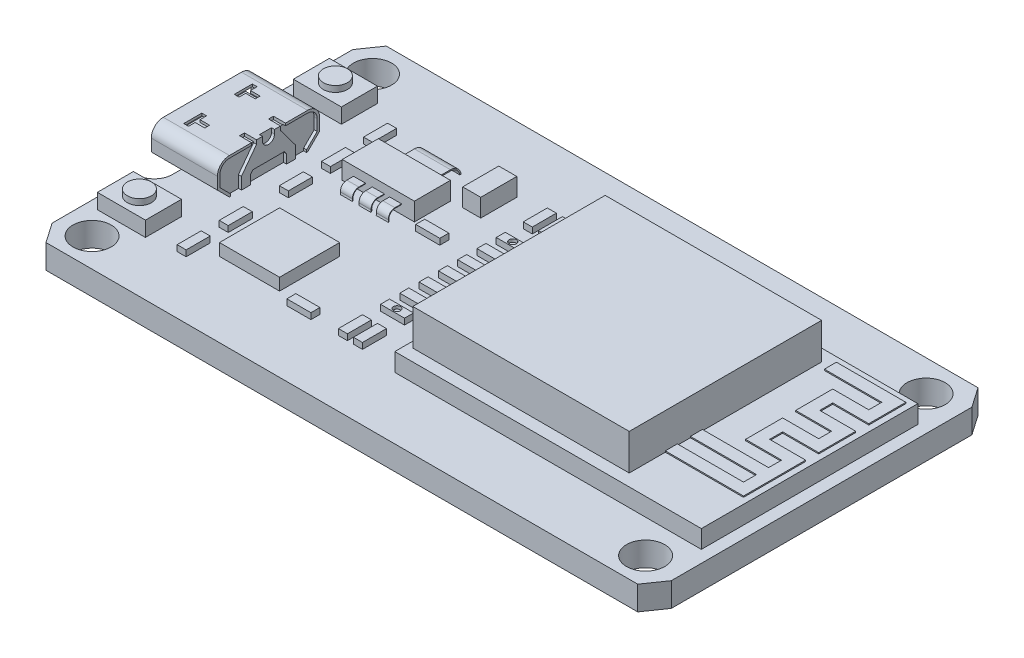
SolidWorks part; units mm, degrees
ref_plane "Alzado" through (0, 0, 0) normal (0, 0, 1) x (1, 0, 0)
ref_plane "Planta" through (0, 0, 0) normal (0, 1, 0) x (1, 0, 0)
ref_plane "Vista lateral" through (0, 0, 0) normal (1, 0, 0) x (0, 0, -1)
sketch "Croquis1" plane through (0, 0, 0) normal (0, 1, 0) x (1, 0, 0)
  line L1 (25.75, 14.15) -> (-25.75, 14.15)
  line L2 (25.75, 14.15) -> (25.75, -14.15)
  line L3 (25.75, -14.15) -> (-25.75, -14.15)
  line L4 (-25.75, 14.15) -> (-25.75, -14.15)
  line L5 (25.75, 14.15) -> (-25.75, -14.15) construction
  line L6 (25.75, -14.15) -> (-25.75, 14.15) construction
  point P0 (0, 0)
  dimension "D1" = 28.3
  dimension "D2" = 51.5
extrude "Saliente-Extruir1" add sketch "Croquis1" along normal blind 2
sketch "Croquis2" plane through (0, 2, 0) normal (0, 1, 0) x (1, 0, 0)
  line L0 (-23.1625, 11.5625) -> (22.875, 11.5625) construction
  line L1 (-23.1625, 11.5625) -> (-25.75, 11.5625) construction
  line L2 (-25.75, 14.15) -> (-25.75, -14.15) construction
  line L3 (-25.75, 11.5625) -> (-24.75, 11.5625) construction
  line L4 (24.4625, 11.5625) -> (25.75, 11.5625) construction
  line L5 (25.75, -14.15) -> (25.75, 14.15) construction
  line L6 (-23.1625, 13.15) -> (-23.1625, 14.15) construction
  line L8 (-23.1625, 11.5625) -> (-23.1625, -11.7625) construction
  line L9 (-23.1625, -11.7625) -> (22.875, -11.7625) construction
  line L10 (25.75, 14.15) -> (-25.75, 14.15) construction
  circle A0 centre (-23.1625, 11.5625) radius 1.5875
  circle A1 centre (22.875, 11.5625) radius 1.5875
  circle A2 centre (-23.1625, -11.7625) radius 1.5875
  circle A3 centre (22.875, -11.7625) radius 1.5875
  point P6 (-0.1437, 11.5625)
  dimension "D1" = 3.175
  dimension "D3" = 1
  dimension "D2" = 46.0375
  dimension "D4" = 1.2875
  dimension "D5" = 23.325
  dimension "D6" = 1
extrude "Cortar-Extruir1" cut sketch "Croquis2" against normal blind 2
sketch "Croquis13" plane through (0, 2, 0) normal (0, 1, 0) x (1, 0, 0)
  line L0 (25.75, 12.5) -> (25.75, -12.5)
  line L1 (25.75, -14.15) -> (25.75, 14.15) construction
  line L2 (-24.6062, -14.15) -> (24.6062, -14.15)
  line L3 (-25.75, -14.15) -> (25.75, -14.15) construction
  line L4 (-24.6062, 14.15) -> (24.6062, 14.15)
  line L5 (25.75, 14.15) -> (-25.75, 14.15) construction
  line L6 (24.6062, 14.15) -> (25.75, 12.5)
  line L7 (25.75, -12.5) -> (24.6062, -14.15)
  line L8 (-25.75, 12.5) -> (-25.75, 5.5)
  line L10 (-25.75, 14.15) -> (-25.75, -14.15) construction
  line L11 (-24.6062, 14.15) -> (-25.75, 12.5)
  line L12 (-25.75, -12.5) -> (-24.6062, -14.15)
  line L13 (-24.25, 4) -> (-24.25, -4)
  line L14 (-25.75, -5.5) -> (-25.75, -12.5)
  arc A0 (-24.25, 4) -> (-25.75, 5.5) centre (-25.75, 4) ccw
  arc A1 (-25.75, -5.5) -> (-24.25, -4) centre (-25.75, -4) ccw
  point P5 (25.75, 0)
  point P11 (0, -14.15)
  point P16 (0, 14.15)
  point P19 (-25.75, 0)
  point P24 (-24.25, 0)
  dimension "D1" = 25
  dimension "D2" = 49.2125
  dimension "D3" = 25
  dimension "D4" = 8
  dimension "D5" = 1.5
extrude "Cortar-Extruir2" cut sketch "Croquis13" against normal blind 3 flip side to cut
sketch "Croquis3" plane through (0, 2, 0) normal (0, 1, 0) x (1, 0, 0)
  line L0 (25.75, -12.5) -> (25.75, 12.5) construction
  line L1 (-0.75, -9) -> (24.75, -9)
  line L2 (-0.75, -9) -> (-0.75, 9)
  line L3 (-0.75, 9) -> (24.75, 9)
  line L4 (24.75, -9) -> (24.75, 9)
  line L5 (-0.75, -9) -> (24.75, 9) construction
  line L6 (-0.75, 9) -> (24.75, -9) construction
  point P0 (12, 0)
  dimension "D1" = 18
  dimension "D2" = 25.5
  dimension "D3" = 1
extrude "Saliente-Extruir2" add sketch "Croquis3" along normal blind 1.5
sketch "Croquis4" plane through (0, 3.5, 0) normal (0, 1, 0) x (1, 0, 0)
  line L0 (17.75, 0) -> (24.75, 0) construction
  line L1 (17.75, 8) -> (-0.25, 8)
  line L2 (17.75, 8) -> (17.75, -8)
  line L3 (17.75, -8) -> (-0.25, -8)
  line L4 (-0.25, 8) -> (-0.25, -8)
  line L5 (17.75, 8) -> (-0.25, -8) construction
  line L6 (17.75, -8) -> (-0.25, 8) construction
  line L7 (24.75, -9) -> (24.75, 9) construction
  point P0 (8.75, 0)
  dimension "D1" = 16
  dimension "D2" = 18
  dimension "D3" = 7
extrude "Saliente-Extruir3" add sketch "Croquis4" along normal blind 3
sketch "Croquis12" plane through (0, 2, 0) normal (0, 1, 0) x (1, 0, 0)
  line L0 (-25.75, 14.15) -> (-25.75, -14.15) construction
  line L1 (-20.25, 4.25) -> (-25.75, 4.25)
  line L2 (-20.25, 4.25) -> (-20.25, -4.25)
  line L3 (-20.25, -4.25) -> (-25.75, -4.25)
  line L4 (-25.75, 4.25) -> (-25.75, -4.25)
  line L5 (-20.25, 4.25) -> (-25.75, -4.25) construction
  line L6 (-20.25, -4.25) -> (-25.75, 4.25) construction
  point P0 (-23, 0)
  dimension "D1" = 8.5
  dimension "D2" = 5.5
extrude "Saliente-Extruir9" add sketch "Croquis12" along normal blind 3
fillet "Redondeo1" radius 1 2 edges at (-23, 5, 4.25) (-23, 5, -4.25)
sketch "Croquis14" plane through (-25.75, 0, 0) normal (-1, 0, 0) x (0, 0, 1)
  line L0 (4.25, 2) -> (3.25, 2) construction
  line L1 (-4, 2) -> (4, 2) construction
  line L2 (3.25, 2) -> (4.25, 3)
  line L3 (4.25, 4) -> (4.25, 2) construction
  line L4 (-4.25, 2) -> (-3.25, 2) construction
  line L5 (-3.25, 2) -> (-4.25, 3)
  line L6 (-4.25, 4) -> (-4.25, 2) construction
  line L7 (-4.25, 3) -> (-4.25, 2)
  line L8 (-4.25, 2) -> (-3.25, 2)
  line L10 (4.25, 3) -> (4.25, 2)
  line M3 (4.25, 2) -> (4.25, 4)
  line M7 (-4.25, 4) -> (-4.25, 2)
  line M8 (-4.25, 2) -> (4.25, 2)
  dimension "D1" = 1
  dimension "D2" = 1
extrude "Cortar-Extruir3" cut sketch "Croquis14" against normal blind 6 contours L5 M8 M7 | L2 M8 M3
sketch "Croquis15" plane through (-25.75, 0, 0) normal (-1, 0, 0) x (0, 0, 1)
  line L0 (-3.25, 2) -> (3.25, 2) construction
  line L1 (3.25, 2) -> (4.25, 3) construction
  line L2 (4.25, 3) -> (4.25, 4) construction
  line L3 (-3.25, 5) -> (3.25, 5) construction
  line L4 (3.25, 5) -> (-3.25, 5) construction
  line L5 (-4.25, 4) -> (-4.25, 3) construction
  line L6 (-4.25, 3) -> (-3.25, 2) construction
  line L7 (-3.25, 2) -> (3.25, 2) construction
  line L8 (-3.1672, 2.2) -> (3.1672, 2.2)
  line L9 (3.1672, 2.2) -> (4.05, 3.0828)
  line L10 (4.05, 3.0828) -> (4.05, 4)
  line L11 (3.25, 4.8) -> (-3.25, 4.8)
  line L12 (-4.05, 4) -> (-4.05, 3.0828)
  line L13 (-4.05, 3.0828) -> (-3.1672, 2.2)
  line L14 (-3.1672, 2.2) -> (3.1672, 2.2)
  line L15 (-3.25, 2.2) -> (3.25, 2.2) construction
  line L16 (-3.25, 2.2) -> (3.25, 2.2) construction
  line L17 (-4.05, 3.0828) -> (-3.1086, 2.1414) construction
  line L18 (3.1086, 2.1414) -> (4.05, 3.0828) construction
  arc A0 (-3.25, 5) -> (-4.25, 4) centre (-3.25, 4) ccw construction
  arc A1 (4.25, 4) -> (3.25, 5) centre (3.25, 4) ccw construction
  arc A2 (-3.25, 5) -> (-4.25, 4) centre (-3.25, 4) ccw construction
  arc A3 (4.05, 4) -> (3.25, 4.8) centre (3.25, 4) ccw
  arc A4 (-3.25, 4.8) -> (-4.05, 4) centre (-3.25, 4) ccw
  point P4 (3.25, 5)
  point P9 (-3.25, 5)
  point P10 (-4.25, 4)
  dimension "D1" = 0.2
extrude "Cortar-Extruir4" cut sketch "Croquis15" against normal blind 4 contours L11 A4 L12 L13 L8 L9 L10 A3
sketch "Croquis16" plane through (-20.25, 0, 0) normal (1, 0, 0) x (0, 0, -1)
  line L0 (-3.25, 2) -> (-3.1672, 2) construction
  line L1 (-1.5, 2.7501) -> (-1.5, 2)
  line L3 (-4.25, 3) -> (-2.25, 3) construction
  line L4 (-2.25, 3) -> (-1, 4.6673)
  line L5 (-0.5, 5) -> (0.5, 5)
  line L6 (-3.25, 5) -> (3.25, 5) construction
  line L7 (3.1672, 2.2) -> (3.1672, 2)
  line L8 (-0.5, 5) -> (-0.5, 4.6673)
  line L9 (0, 5) -> (0, 2.5205) construction
  line L10 (-1, 4.6673) -> (-1, 5)
  line L11 (-3.25, 2) -> (-4.25, 3) construction
  line L12 (-4.25, 3) -> (-4.25, 4) construction
  line L13 (-3.25, 5) -> (-1.4111, 5) construction
  line L19 (-3.1672, 2.2) -> (-4.05, 3.0828)
  line L20 (-4.05, 3.0828) -> (-4.05, 4)
  line L21 (-2.45, 3.0666) -> (-1.2, 4.7339) construction
  line L22 (-1.2, 4.7339) -> (-1.2, 4.8) construction
  line L23 (-2.45, 2.2) -> (-2.45, 3.0666) construction
  line L25 (-3.1672, 2.2) -> (-2.45, 2.2) construction
  line L26 (-2.25, 2) -> (-2.25, 3) construction
  line L27 (-3.25, 4.8) -> (-1.2, 4.8) construction
  line L28 (-3.25, 4.8) -> (-1.4111, 4.8)
  line L31 (-3.25, 5) -> (-1, 5) construction
  line L33 (-1.4111, 4.8) -> (-1.4111, 5)
  line L34 (-1.4111, 5) -> (-1, 5)
  line L35 (-1.5, 2.7501) -> (-1.3169, 2.9943)
  line L36 (-1.3169, 2.9943) -> (1.3169, 2.9943)
  line L37 (-1.5, 2.7501) -> (-0.3999, 4.2174) construction
  line L39 (3.25, 5) -> (1.4111, 5) construction
  line L40 (4.25, 3) -> (4.25, 4) construction
  line L41 (3.25, 2) -> (4.25, 3) construction
  line L43 (4.25, 3) -> (2.25, 3) construction
  line L44 (3.25, 2) -> (3.1672, 2) construction
  line L45 (1.5, 2.7501) -> (1.3169, 2.9943)
  line L46 (1.4111, 5) -> (1, 5)
  line L47 (1.4111, 4.8) -> (1.4111, 5)
  line L49 (3.25, 4.8) -> (1.4111, 4.8)
  line L51 (4.05, 3.0828) -> (4.05, 4)
  line L52 (3.1672, 2.2) -> (4.05, 3.0828)
  line L53 (1, 4.6673) -> (1, 5)
  line L54 (0.5, 5) -> (0.5, 4.6673)
  line L55 (2.25, 3) -> (1, 4.6673)
  line L57 (3.1672, 2) -> (2.25, 2)
  line L58 (2.25, 3) -> (2.25, 2)
  line L59 (-3.1672, 2.2) -> (-3.1672, 2)
  line L60 (-2.25, 3) -> (-2.25, 2)
  line L61 (-3.25, 2) -> (3.25, 2) construction
  line L62 (-3.25, 2) -> (-2.25, 2) construction
  line L63 (-2.25, 2.2) -> (-2.25, 3) construction
  line L64 (-2.25, 2) -> (-3.1672, 2)
  line L66 (1.5, 2) -> (-1.5, 2)
  line L68 (-1.5, 2.2) -> (-1.5, 2.7501) construction
  line L69 (1.5, 2.7501) -> (1.5, 2)
  arc A0 (-0.5, 4.6673) -> (0.5, 4.6673) centre (0, 4.6673) ccw
  arc A1 (-4.25, 4) -> (-3.25, 5) centre (-3.25, 4) cw construction
  arc A2 (-4.05, 4) -> (-3.25, 4.8) centre (-3.25, 4) cw
  arc A3 (4.25, 4) -> (3.25, 5) centre (3.25, 4) ccw construction
  arc A4 (4.05, 4) -> (3.25, 4.8) centre (3.25, 4) ccw
  point P50 (0, 5)
  point P57 (0, 2.2)
  point P58 (0, 2.9943)
  dimension "D2" = 0.5
  dimension "D3" = 0.5
  dimension "D4" = 0.2
  dimension "D5" = 0.75
extrude "Cortar-Extruir5" cut sketch "Croquis16" against normal blind 0.25
sketch "Croquis17" plane through (0, 5, 0) normal (0, 1, 0) x (1, 0, 0)
  line L1 (-20.25, -1.4111) -> (-21.25, -1.4111)
  line L2 (-20.25, -1.4111) -> (-20.25, -1)
  line L3 (-20.25, -1) -> (-21.25, -1)
  line L4 (-21.25, -1.4111) -> (-21.25, -1)
  line L5 (-20.25, 1) -> (-21.25, 1)
  line L6 (-20.25, 1) -> (-20.25, 1.4111)
  line L7 (-20.25, 1.4111) -> (-21.25, 1.4111)
  line L8 (-21.25, 1) -> (-21.25, 1.4111)
  dimension "D1" = 1
extrude "Cortar-Extruir6" cut sketch "Croquis17" against normal blind 0.25
sketch "Croquis18" plane through (-21.75, 0, 0) normal (-1, 0, 0) x (0, 0, 1)
  line L1 (-2.8448, 3.4346) -> (2.8448, 3.4346)
  line L2 (-2.8448, 3.4346) -> (-2.8448, 4.1935)
  line L3 (-2.8448, 4.1935) -> (2.8448, 4.1935)
  line L4 (2.8448, 3.4346) -> (2.8448, 4.1935)
  line L5 (-2.8448, 3.4346) -> (2.8448, 4.1935) construction
  line L6 (-2.8448, 4.1935) -> (2.8448, 3.4346) construction
  point P0 (0, 3.8141)
extrude "Saliente-Extruir10" add sketch "Croquis18" along normal blind 3.25
sketch "Croquis19" plane through (0, 2, 0) normal (0, 1, 0) x (1, 0, 0)
  line L0 (-24.6062, -14.15) -> (24.6062, -14.15) construction
  line L1 (-24.8373, -6.65) -> (-20.8373, -6.65)
  line L2 (-24.8373, -6.65) -> (-24.8373, -9.65)
  line L3 (-24.8373, -9.65) -> (-20.8373, -9.65)
  line L4 (-20.8373, -6.65) -> (-20.8373, -9.65)
  line L5 (-24.8373, -6.65) -> (-20.8373, -9.65) construction
  line L6 (-24.8373, -9.65) -> (-20.8373, -6.65) construction
  line L7 (24.6062, 14.15) -> (-24.6062, 14.15) construction
  line L8 (-24.8373, 9.65) -> (-20.8373, 9.65)
  line L9 (-24.8373, 9.65) -> (-24.8373, 6.65)
  line L10 (-24.8373, 6.65) -> (-20.8373, 6.65)
  line L11 (-20.8373, 9.65) -> (-20.8373, 6.65)
  line L12 (-24.8373, 9.65) -> (-20.8373, 6.65) construction
  line L13 (-24.8373, 6.65) -> (-20.8373, 9.65) construction
  point P0 (-22.8373, -8.15)
  point P7 (-22.8373, 8.15)
  dimension "D1" = 4.5
  dimension "D2" = 3
  dimension "D3" = 4
  dimension "D4" = 3
  dimension "D5" = 4.5
extrude "Saliente-Extruir11" add sketch "Croquis19" along normal blind 1.25
sketch "Croquis22" plane through (0, 3.25, 0) normal (0, 1, 0) x (1, 0, 0)
  line L0 (-22.8373, 9.65) -> (-22.8373, 6.65) construction
  line L1 (-20.8373, 9.65) -> (-24.8373, 9.65) construction
  line L2 (-24.8373, 6.65) -> (-20.8373, 6.65) construction
  line L3 (-22.8373, -6.65) -> (-22.8373, -9.65) construction
  line L4 (-20.8373, -6.65) -> (-24.8373, -6.65) construction
  line L5 (-24.8373, -9.65) -> (-20.8373, -9.65) construction
  circle A0 centre (-22.8373, 8.15) radius 1
  circle A1 centre (-22.8373, -8.15) radius 1
  dimension "D1" = 2
  dimension "D2" = 2
extrude "Saliente-Extruir13" add sketch "Croquis22" along normal blind 0.5
sketch "Croquis23" plane through (0, 2, 0) normal (0, 1, 0) x (1, 0, 0)
  line L0 (-18.125, 8.15) -> (-18.125, -0.85) construction
  line L1 (-18.125, 8.15) -> (-18.125, 14.15) construction
  line L2 (-18.5, 4.65) -> (-17.75, 4.65)
  line L3 (-18.5, 4.65) -> (-18.5, 2.65)
  line L4 (-18.5, 2.65) -> (-17.75, 2.65)
  line L5 (-17.75, 4.65) -> (-17.75, 2.65)
  line L6 (-18.5, 4.65) -> (-17.75, 2.65) construction
  line L7 (-18.5, 2.65) -> (-17.75, 4.65) construction
  line L8 (-17.75, 6.15) -> (-18.5, 6.15)
  line L9 (-17.75, 6.15) -> (-17.75, 8.15)
  line L10 (-17.75, 8.15) -> (-18.5, 8.15)
  line L11 (-18.5, 6.15) -> (-18.5, 8.15)
  line L12 (-17.75, 6.15) -> (-18.5, 8.15) construction
  line L13 (-17.75, 8.15) -> (-18.5, 6.15) construction
  line L14 (-17.75, 1.15) -> (-18.5, 1.15)
  line L15 (-17.75, 1.15) -> (-17.75, -0.85)
  line L16 (-17.75, -0.85) -> (-18.5, -0.85)
  line L17 (-18.5, 1.15) -> (-18.5, -0.85)
  line L18 (-17.75, 1.15) -> (-18.5, -0.85) construction
  line L19 (-17.75, -0.85) -> (-18.5, 1.15) construction
  line L20 (24.6062, 14.15) -> (-24.6062, 14.15) construction
  line L21 (-25.75, 12.5) -> (-25.75, 5.5) construction
  line L22 (-18.125, -3.85) -> (-18.125, -9.35) construction
  line L23 (-18.5, -7.35) -> (-17.75, -7.35)
  line L24 (-18.5, -7.35) -> (-18.5, -9.35)
  line L25 (-18.5, -9.35) -> (-17.75, -9.35)
  line L26 (-17.75, -7.35) -> (-17.75, -9.35)
  line L27 (-18.5, -7.35) -> (-17.75, -9.35) construction
  line L28 (-18.5, -9.35) -> (-17.75, -7.35) construction
  line L29 (-17.75, -5.85) -> (-18.5, -5.85)
  line L30 (-17.75, -5.85) -> (-17.75, -3.85)
  line L31 (-17.75, -3.85) -> (-18.5, -3.85)
  line L32 (-18.5, -5.85) -> (-18.5, -3.85)
  line L33 (-17.75, -5.85) -> (-18.5, -3.85) construction
  line L34 (-17.75, -3.85) -> (-18.5, -5.85) construction
  line L39 (-4.75, 5.1875) -> (-4.75, -4.8125) construction
  line L40 (-5.75, 3.5833) -> (-3.75, 3.5833)
  line L41 (-5.75, 4.4375) -> (-3.75, 4.4375)
  line L42 (-5.75, 4.4375) -> (-5.75, 5.1875)
  line L43 (-5.75, 5.1875) -> (-3.75, 5.1875)
  line L44 (-3.75, 4.4375) -> (-3.75, 5.1875)
  line L45 (-5.75, 4.4375) -> (-3.75, 5.1875) construction
  line L46 (-5.75, 5.1875) -> (-3.75, 4.4375) construction
  line L47 (-5.75, 2.8333) -> (-3.75, 2.8333)
  line L48 (-5.75, 2.8333) -> (-5.75, 3.5833)
  line L49 (-3.75, 2.8333) -> (-3.75, 3.5833)
  line L50 (-5.75, 1.9792) -> (-3.75, 1.9792)
  line L51 (-5.75, 1.2292) -> (-3.75, 1.2292)
  line L52 (-5.75, 1.2292) -> (-5.75, 1.9792)
  line L53 (-3.75, 1.2292) -> (-3.75, 1.9792)
  line L54 (-5.75, 0.375) -> (-3.75, 0.375)
  line L55 (-5.75, -0.375) -> (-3.75, -0.375)
  line L56 (-5.75, -0.375) -> (-5.75, 0.375)
  line L57 (-3.75, -0.375) -> (-3.75, 0.375)
  line L58 (-5.75, -1.2292) -> (-3.75, -1.2292)
  line L59 (-5.75, -1.9792) -> (-3.75, -1.9792)
  line L60 (-5.75, -1.9792) -> (-5.75, -1.2292)
  line L61 (-3.75, -1.9792) -> (-3.75, -1.2292)
  line L62 (-5.75, -2.8333) -> (-3.75, -2.8333)
  line L63 (-5.75, -3.5833) -> (-3.75, -3.5833)
  line L64 (-5.75, -3.5833) -> (-5.75, -2.8333)
  line L65 (-3.75, -3.5833) -> (-3.75, -2.8333)
  line L66 (-5.75, -4.4375) -> (-3.75, -4.4375)
  line L67 (-5.75, -5.1875) -> (-3.75, -5.1875)
  line L68 (-5.75, -5.1875) -> (-5.75, -4.4375)
  line L69 (-3.75, -5.1875) -> (-3.75, -4.4375)
  line L70 (-0.75, 9) -> (-0.75, -9) construction
  line L72 (-4.5, -6.6875) -> (-3.75, -6.6875)
  line L73 (-4.5, -6.6875) -> (-4.5, -8.6875)
  line L74 (-4.5, -8.6875) -> (-3.75, -8.6875)
  line L75 (-3.75, -6.6875) -> (-3.75, -8.6875)
  line L76 (-4.5, -6.6875) -> (-3.75, -8.6875) construction
  line L77 (-4.5, -8.6875) -> (-3.75, -6.6875) construction
  line L79 (-5.75, -6.6875) -> (-5, -6.6875)
  line L80 (-5.75, -6.6875) -> (-5.75, -8.6875)
  line L81 (-5.75, -8.6875) -> (-5, -8.6875)
  line L82 (-5, -6.6875) -> (-5, -8.6875)
  line L83 (-5.75, -6.6875) -> (-5, -8.6875) construction
  line L84 (-5.75, -8.6875) -> (-5, -6.6875) construction
  line L85 (-4.75, 5.1875) -> (-4.75, -5.1875) construction
  line L86 (-4.75, 2.8333) -> (-4.75, 1.9792) construction
  line L87 (-4.5, 8.6875) -> (-3.75, 8.6875)
  line L88 (-4.5, 8.6875) -> (-4.5, 6.6875)
  line L89 (-4.5, 6.6875) -> (-3.75, 6.6875)
  line L90 (-3.75, 8.6875) -> (-3.75, 6.6875)
  line L91 (-4.5, 8.6875) -> (-3.75, 6.6875) construction
  line L92 (-4.5, 6.6875) -> (-3.75, 8.6875) construction
  line L93 (-5.75, 8.6875) -> (-5, 8.6875)
  line L94 (-5.75, 8.6875) -> (-5.75, 6.6875)
  line L95 (-5.75, 6.6875) -> (-5, 6.6875)
  line L96 (-5, 8.6875) -> (-5, 6.6875)
  line L97 (-5.75, 8.6875) -> (-5, 6.6875) construction
  line L98 (-5.75, 6.6875) -> (-5, 8.6875) construction
  line L99 (-10.0373, -7.9375) -> (-8.0373, -7.9375)
  line L100 (-10.0373, -7.9375) -> (-10.0373, -8.6875)
  line L101 (-10.0373, -8.6875) -> (-8.0373, -8.6875)
  line L102 (-8.0373, -7.9375) -> (-8.0373, -8.6875)
  line L103 (-10.0373, -7.9375) -> (-8.0373, -8.6875) construction
  line L104 (-10.0373, -8.6875) -> (-8.0373, -7.9375) construction
  line L106 (-10.0373, 2.7812) -> (-8.0373, 2.7812)
  line L107 (-10.0373, 2.7812) -> (-10.0373, 2.0312)
  line L108 (-10.0373, 2.0312) -> (-8.0373, 2.0312)
  line L109 (-8.0373, 2.7812) -> (-8.0373, 2.0312)
  line L110 (-10.0373, 2.7812) -> (-8.0373, 2.0312) construction
  line L111 (-10.0373, 2.0312) -> (-8.0373, 2.7812) construction
  point P2 (-18.125, 3.65)
  point P7 (-18.125, 7.15)
  point P12 (-18.125, 0.15)
  point P24 (-18.125, -8.35)
  point P29 (-18.125, -4.85)
  point P35 (-4.75, 4.8125)
  point P42 (-4.75, 3.2083)
  point P47 (-4.75, 1.6042)
  point P52 (-4.75, 0)
  point P57 (-4.75, -1.6042)
  point P62 (-4.75, -3.2083)
  point P67 (-4.75, -4.8125)
  point P73 (-5.375, -7.6875)
  point P74 (-4.125, -7.6875)
  point P83 (-5.375, 7.6875)
  point P84 (-4.125, 7.6875)
  point P97 (-4.75, 2.4062)
  point P98 (-9.0373, -8.3125)
  point P103 (-9.0373, 2.4062)
  dimension "D1" = 9
  dimension "D2" = 0.75
  dimension "D3" = 2
  dimension "D4" = 6
  dimension "D5" = 8
  dimension "D6" = 2
  dimension "D7" = 2
  dimension "D8" = 1.5
  dimension "D9" = 3
  dimension "D10" = 0.75
  dimension "D11" = 7
  dimension "D12" = 10
  dimension "D13" = 0.75
  dimension "D14" = 4
  dimension "D15" = 0.75
  dimension "D16" = 2
  dimension "D17" = 2
  dimension "D18" = 1.5
  dimension "D19" = 1.5
  dimension "D20" = 0.75
  dimension "D21" = 2
extrude "Saliente-Extruir14" add sketch "Croquis23" along normal blind 0.5
sketch "Croquis26" plane through (0, 2, 0) normal (0, 1, 0) x (1, 0, 0)
  line L0 (-8.0373, -7.9375) -> (-10.0373, -7.9375) construction
  line L1 (-16.3937, -2.9375) -> (-11.3937, -2.9375)
  line L2 (-16.3937, -2.9375) -> (-16.3937, -7.9375)
  line L3 (-16.3937, -7.9375) -> (-11.3937, -7.9375)
  line L4 (-11.3937, -2.9375) -> (-11.3937, -7.9375)
  line L5 (-16.3937, -2.9375) -> (-11.3937, -7.9375) construction
  line L6 (-16.3937, -7.9375) -> (-11.3937, -2.9375) construction
  line L7 (-17.75, -8.35) -> (-10.0373, -8.3125) construction
  line L8 (-17.75, -9.35) -> (-17.75, -7.35) construction
  line L9 (-10.0373, -7.9375) -> (-10.0373, -8.6875) construction
  point P0 (-13.8937, -5.4375)
  point P7 (-13.8937, -8.3312)
  dimension "D1" = 5
  dimension "D2" = 5
extrude "Saliente-Extruir15" add sketch "Croquis26" along normal blind 1
sketch "Croquis27" plane through (0, 2, 0) normal (0, 1, 0) x (1, 0, 0)
  line L0 (-8.0373, 2.7812) -> (-10.0373, 2.7812) construction
  line L1 (-5, 8.6875) -> (-5.75, 8.6875) construction
  line L2 (-9.7873, 8.6875) -> (-8.2873, 8.6875)
  line L3 (-9.7873, 8.6875) -> (-9.7873, 5.6875)
  line L4 (-9.7873, 5.6875) -> (-8.2873, 5.6875)
  line L5 (-8.2873, 8.6875) -> (-8.2873, 5.6875)
  line L6 (-9.7873, 8.6875) -> (-8.2873, 5.6875) construction
  line L7 (-9.7873, 5.6875) -> (-8.2873, 8.6875) construction
  point P0 (-9.0373, 2.7812)
  point P1 (-9.0373, 7.1875)
  dimension "D1" = 1.5
  dimension "D2" = 3
extrude "Saliente-Extruir16" add sketch "Croquis27" along normal blind 1.5
sketch "Croquis28" plane through (0, 2, 0) normal (0, 1, 0) x (1, 0, 0)
  line L0 (-17.75, 8.15) -> (-9.7873, 8.15) construction
  line L1 (-16.7687, 5.65) -> (-10.7687, 5.65)
  line L2 (-16.7687, 5.65) -> (-16.7687, 2.65)
  line L3 (-16.7687, 2.65) -> (-10.7687, 2.65)
  line L4 (-10.7687, 5.65) -> (-10.7687, 2.65)
  line L5 (-16.7687, 5.65) -> (-10.7687, 2.65) construction
  line L6 (-16.7687, 2.65) -> (-10.7687, 5.65) construction
  line L7 (-9.7873, 8.6875) -> (-9.7873, 5.6875) construction
  line L9 (-18.5, 2.65) -> (-17.75, 2.65) construction
  point P0 (-13.7687, 4.15)
  point P10 (-13.7687, 8.15)
  dimension "D1" = 6
  dimension "D2" = 3
extrude "Saliente-Extruir17" add sketch "Croquis28" along normal blind 1.5
sketch "Croquis30" plane through (0, 3.5, 0) normal (0, 1, 0) x (1, 0, 0)
  line L0 (18.4797, 8) -> (23.7544, 8) construction
  line L1 (23.7544, 8) -> (23.7544, 5.9167) construction
  line L2 (23.7544, 5.9167) -> (20.7587, 5.9167) construction
  line L3 (20.7587, 5.9167) -> (20.7587, 3.8333) construction
  line L4 (20.7587, 3.8333) -> (23.7544, 3.8333) construction
  line L5 (23.7544, 3.8333) -> (23.7544, 1.75) construction
  line L6 (23.7544, 1.75) -> (20.7587, 1.75) construction
  line L7 (20.7587, 1.75) -> (20.7587, -0.3333) construction
  line L8 (20.7587, -0.3333) -> (23.7544, -0.3333) construction
  line L9 (23.7544, -0.3333) -> (23.7544, -2.4167) construction
  line L10 (23.7544, -2.4167) -> (23.7544, -4.5) construction
  line L11 (23.7544, -4.5) -> (17.75, -4.5) construction
  line L12 (17.75, -8) -> (17.75, 8) construction
  line L13 (23.7544, -2.4167) -> (17.75, -2.4167) construction
  line L14 (17.75, 8) -> (-0.25, 8) construction
  line L15 (18.4797, 7.5) -> (23.2544, 7.5)
  line L16 (23.2544, 7.5) -> (23.2544, 6.4167)
  line L17 (23.2544, 6.4167) -> (20.2587, 6.4167)
  line L18 (20.2587, 6.4167) -> (20.2587, 3.3333)
  line L19 (20.2587, 3.3333) -> (23.2544, 3.3333)
  line L20 (23.2544, 3.3333) -> (23.2544, 2.25)
  line L21 (23.2544, 2.25) -> (20.2587, 2.25)
  line L22 (20.2587, 2.25) -> (20.2587, -0.8333)
  line L23 (20.2587, -0.8333) -> (23.2544, -0.8333)
  line L24 (23.2544, -0.8333) -> (23.2544, -1.9167)
  line L25 (23.2544, -2.9167) -> (23.2544, -4)
  line L26 (23.2544, -4) -> (17.75, -4)
  line L27 (23.2544, -1.9167) -> (17.75, -1.9167)
  line L28 (18.4797, 8.5) -> (24.2544, 8.5)
  line L29 (24.2544, 8.5) -> (24.2544, 5.4167)
  line L30 (24.2544, 5.4167) -> (21.2587, 5.4167)
  line L31 (21.2587, 5.4167) -> (21.2587, 4.3333)
  line L32 (21.2587, 4.3333) -> (24.2544, 4.3333)
  line L33 (24.2544, 4.3333) -> (24.2544, 1.25)
  line L34 (24.2544, 1.25) -> (21.2587, 1.25)
  line L35 (21.2587, 1.25) -> (21.2587, 0.1667)
  line L36 (21.2587, 0.1667) -> (24.2544, 0.1667)
  line L37 (24.2544, 0.1667) -> (24.2544, -2.4167)
  line L38 (24.2544, -2.4167) -> (24.2544, -5)
  line L39 (24.2544, -5) -> (17.75, -5)
  line L40 (23.2544, -2.9167) -> (17.75, -2.9167)
  line L41 (23.2544, -2.4167) -> (23.2544, -4) construction
  line L42 (23.2544, -0.8333) -> (23.2544, -2.4167) construction
  line L43 (23.7544, -1.9167) -> (17.75, -1.9167) construction
  line L44 (23.7544, -2.9167) -> (17.75, -2.9167) construction
  line L45 (18.4797, 8.5) -> (18.4797, 7.5)
  line L46 (17.75, -1.9167) -> (17.75, -2.9167)
  line L47 (17.75, -4) -> (17.75, -5)
  point P17 (21.1171, 8)
  dimension "D1" = 12.5
  dimension "D2" = 2.0833
  dimension "D3" = 0.5
  dimension "D4" = 0.5
extrude "Saliente-Extruir18" add sketch "Croquis30" along normal blind 0.1
sketch "Croquis31" plane through (0, 2.5, 0) normal (0, 1, 0) x (1, 0, 0)
  line L0 (-4.75, 5.1875) -> (-4.75, 4.4375) construction
  line L1 (-3.75, 5.1875) -> (-5.75, 5.1875) construction
  line L2 (-5.75, 4.4375) -> (-3.75, 4.4375) construction
  line L3 (-4.75, -4.4375) -> (-4.75, -5.1875) construction
  line L4 (-3.75, -4.4375) -> (-5.75, -4.4375) construction
  line L5 (-5.75, -5.1875) -> (-3.75, -5.1875) construction
  circle A0 centre (-4.75, 4.8125) radius 0.3
  circle A1 centre (-4.75, -4.8125) radius 0.3
  dimension "D1" = 0.6
extrude "Cortar-Extruir7" cut sketch "Croquis31" against normal blind 0.25
ref_plane "Plano2" through (-13.7687, 0, 0) normal (-1, 0, 0) x (0, 0, 1)
sketch "Croquis32" plane through (-13.7687, 0, 0) normal (-1, 0, 0) x (0, 0, 1)
  line L0 (-5.65, 2.75) -> (-7.1537, 2.75)
  line L2 (-5.65, 3.5) -> (-5.65, 2) construction
  arc A0 (-7.1537, 2.75) -> (-8.0258, 1.8778) centre (-7.1537, 1.8778) ccw
sketch "Croquis33" plane through (0, 0, -5.65) normal (0, 0, -1) x (-1, 0, 0)
  line L0 (13.7687, 1.8778) -> (13.7687, 2.75) construction
  line L1 (12.2687, 2.6649) -> (15.2687, 2.6649)
  line L2 (12.2687, 2.6649) -> (12.2687, 2.7649)
  line L3 (12.2687, 2.7649) -> (15.2687, 2.7649)
  line L4 (15.2687, 2.6649) -> (15.2687, 2.7649)
  line L5 (12.2687, 2.6649) -> (15.2687, 2.7649) construction
  line L6 (12.2687, 2.7649) -> (15.2687, 2.6649) construction
  point P0 (13.7687, 2.7149)
  dimension "D1" = 3
  dimension "D2" = 0.1
sweep "Barrer1" add profiles "Croquis33" path "Croquis32"
sketch "Croquis34" plane through (-13.7687, 0, 0) normal (-1, 0, 0) x (0, 0, 1)
  line L0 (-2.65, 2.75) -> (-2.0959, 2.75)
  line L1 (-2.65, 3.5) -> (-2.65, 2) construction
  arc A0 (-2.0959, 2.75) -> (-1.5811, 2.1692) centre (-2.0959, 2.2314) cw
  arc A1 (-1.5811, 2.1692) -> (-1.0864, 1.8337) centre (-1.2473, 2.1289) ccw
sketch "Croquis35" plane through (0, 0, -2.65) normal (0, 0, 1) x (1, 0, 0)
  line L0 (-13.7687, 0.825) -> (-13.7687, -0.825) construction
  line L1 (-14.2687, 2.7235) -> (-13.2687, 2.7235)
  line L2 (-14.2687, 2.7235) -> (-14.2687, 2.7735)
  line L3 (-14.2687, 2.7735) -> (-13.2687, 2.7735)
  line L4 (-13.2687, 2.7235) -> (-13.2687, 2.7735)
  line L5 (-14.2687, 2.7235) -> (-13.2687, 2.7735) construction
  line L6 (-14.2687, 2.7735) -> (-13.2687, 2.7235) construction
  line L7 (-16.3937, 2.7235) -> (-14.2687, 2.7485) construction
  line L8 (-16.3937, 3) -> (-16.3937, 2) construction
  line L9 (-13.2687, 2.7485) -> (-11.3937, 2.7485) construction
  line L10 (-15.8312, 2.711) -> (-14.8312, 2.711)
  line L11 (-15.8312, 2.711) -> (-15.8312, 2.761)
  line L12 (-15.8312, 2.761) -> (-14.8312, 2.761)
  line L13 (-14.8312, 2.711) -> (-14.8312, 2.761)
  line L14 (-15.8312, 2.711) -> (-14.8312, 2.761) construction
  line L15 (-15.8312, 2.761) -> (-14.8312, 2.711) construction
  line L16 (-11.3937, 3) -> (-11.3937, 2) construction
  line L18 (-12.8312, 2.7235) -> (-11.8312, 2.7235)
  line L19 (-12.8312, 2.7235) -> (-12.8312, 2.7735)
  line L20 (-12.8312, 2.7735) -> (-11.8312, 2.7735)
  line L21 (-11.8312, 2.7235) -> (-11.8312, 2.7735)
  line L22 (-12.8312, 2.7235) -> (-11.8312, 2.7735) construction
  line L23 (-12.8312, 2.7735) -> (-11.8312, 2.7235) construction
  point P0 (-13.7687, 2.7485)
  point P11 (-15.3312, 2.736)
  point P12 (-15.3312, 2.736)
  point P21 (-12.3312, 2.7485)
  point P22 (-12.3312, 2.7485)
  dimension "D1" = 1
  dimension "D2" = 0.05
sweep "Barrer2" add profiles "Croquis35" path "Croquis34"
sketch "Croquis36" plane through (0, 5, 0) normal (0, 1, 0) x (1, 0, 0)
  line L0 (-24.25, -2.85) -> (-24.25, -1.35) construction
  line L1 (-25.75, -3.25) -> (-20.25, -3.25) construction
  line L3 (-25.75, 3.25) -> (-25.75, -3.25) construction
  line L4 (-24.25, -2.1) -> (-23.25, -2.1) construction
  line L5 (-24.25, 2.1) -> (-23.25, 2.1) construction
  line L6 (-24.25, -2.85) -> (-24.25, -1.35) construction
  line L7 (-24.25, 1.35) -> (-24.25, 2.85) construction
  line L8 (-24.25, 1.35) -> (-24.25, 2.85) construction
  line L9 (-24.05, -2.3) -> (-23.25, -2.3)
  line L10 (-24.05, -2.85) -> (-24.05, -2.3)
  line L11 (-24.05, 1.35) -> (-24.05, 1.9)
  line L12 (-24.05, 1.9) -> (-23.25, 1.9)
  line L13 (-24.05, -1.9) -> (-23.25, -1.9)
  line L14 (-24.45, -2.85) -> (-24.45, -1.35)
  line L15 (-24.45, 1.35) -> (-24.45, 2.85)
  line L16 (-24.05, 2.3) -> (-23.25, 2.3)
  line L17 (-24.05, -2.85) -> (-24.45, -2.85)
  line L18 (-24.05, -1.35) -> (-24.45, -1.35)
  line L19 (-23.25, -2.3) -> (-23.25, -1.9)
  line L20 (-23.25, 1.9) -> (-23.25, 2.3)
  line L21 (-24.05, 1.35) -> (-24.45, 1.35)
  line L22 (-24.45, 2.85) -> (-24.05, 2.85)
  line L23 (-24.25, -2.3) -> (-23.25, -2.3) construction
  line L24 (-24.25, -2.1) -> (-23.25, -2.1) construction
  line L25 (-24.25, -1.9) -> (-23.25, -1.9) construction
  line L26 (-24.05, -1.9) -> (-24.05, -1.35)
  line L27 (-24.05, -2.85) -> (-24.05, -1.35) construction
  line L28 (-24.25, 1.9) -> (-23.25, 1.9) construction
  line L29 (-24.25, 2.3) -> (-23.25, 2.3) construction
  line L30 (-24.05, 2.3) -> (-24.05, 2.85)
  line L31 (-24.05, 1.35) -> (-24.05, 2.85) construction
  point P15 (-24.25, -2.1)
  point P18 (-24.25, 2.1)
  dimension "D1" = 1.5
  dimension "D2" = 1
  dimension "D3" = 1.5
  dimension "D4" = 1.5
  dimension "D5" = 0.4
  dimension "D6" = 0.2
  dimension "D7" = 0.2
extrude "Cortar-Extruir8" cut sketch "Croquis36" against normal blind 0.5
